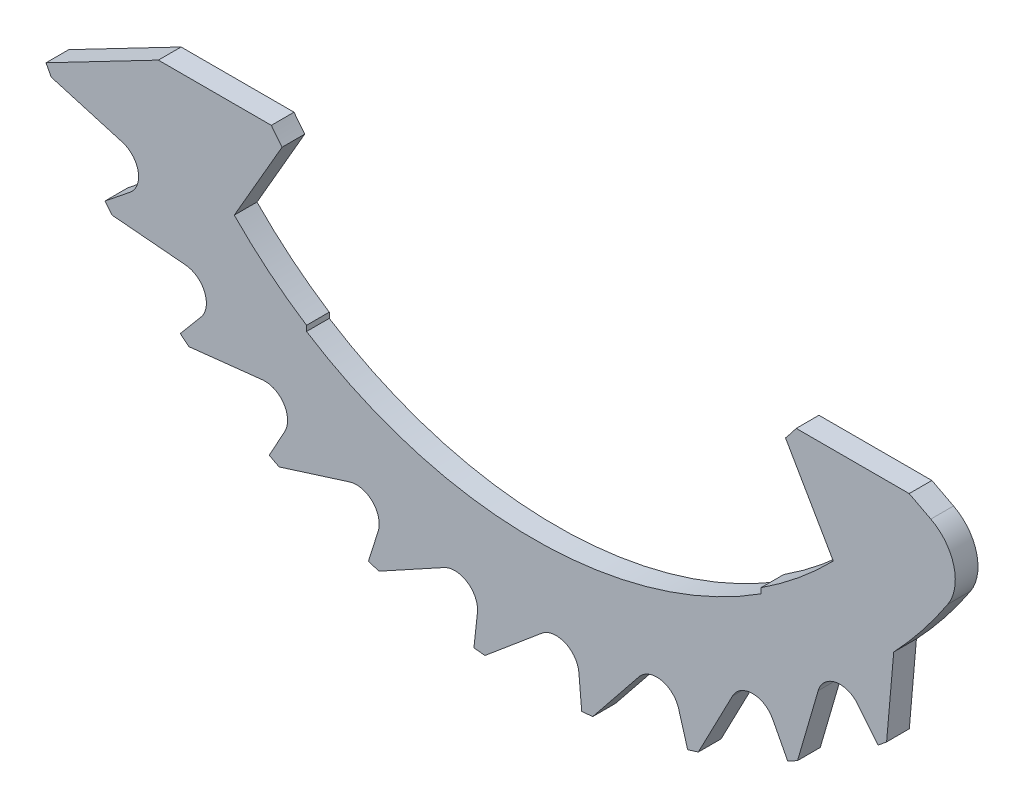
SolidWorks part; units mm, degrees
ref_plane "Front Plane" through (0, 0, 0) normal (0, 0, 1) x (1, 0, 0)
ref_plane "Top Plane" through (0, 0, 0) normal (0, 1, 0) x (1, 0, 0)
ref_plane "Right Plane" through (0, 0, 0) normal (1, 0, 0) x (0, 0, -1)
sketch "Sketch1" plane through (0, 0, 0) normal (0, 0, 1) x (1, 0, 0)
  line L0 (-8.2602, -4.3) -> (-10.7328, -5.5872)
  line L1 (0, 0) -> (0, -12.1) construction
  line L2 (8.2602, -4.3) -> (10.7328, -5.5872)
  line L3 (-5.5392, -4.5997) -> (-6.59, -6.4196)
  line L4 (-8.2602, -4.3) -> (-5.7749, -4.3)
  line L5 (-5, -7.7227) -> (-5, -7.8416)
  line L6 (5.5392, -4.5997) -> (6.59, -6.4196)
  line L8 (-5, 0) -> (-5, -17.1) construction
  line L9 (-5, -17.1) -> (12.3158, -17.1) construction
  line L11 (5, -7.7227) -> (5, -7.8416)
  line L12 (0, -12.1) -> (12.3158, -12.1) construction
  line L13 (5.7749, -4.3) -> (8.2602, -4.3)
  arc A0 (5.7749, -4.3) -> (5.5392, -4.5997) centre (0, 0) cw
  arc A1 (-6.59, -6.4196) -> (-5, -7.7227) centre (0, 0) ccw
  arc A2 (-10.016, -4.3) -> (10.016, -4.3) centre (0, 0) ccw construction
  arc A3 (-10.7328, -5.5872) -> (10.7328, -5.5872) centre (0, 0) ccw
  arc A4 (5, -7.7227) -> (6.59, -6.4196) centre (0, 0) ccw
  circle A5 centre (0, 0) radius 12.1 construction
  circle A6 centre (0, 0) radius 9.2 construction
  arc A7 (-5, -7.8416) -> (5, -7.8416) centre (0, 0) ccw
  arc A8 (-5.7749, -4.3) -> (-5.5392, -4.5997) centre (0, 0) ccw
  point P1 (8.798, 2.6898)
  point P13 (12.1, 0)
  dimension "D1" = 9.3
  dimension "D2" = 9.2
  dimension "D3" = 10.9
  dimension "D10" = 7.2
  dimension "D4" = 2.9
  dimension "D5" = 125
  dimension "D6" = 7.8
  dimension "D9" = 13.18
  dimension "D8" = 30
  dimension "D7" = 10
extrude "Boss-Extrude1" add sketch "Sketch1" along normal blind 0.5
sketch "Sketch2" plane through (0, 0, 0.5) normal (0, 0, 1) x (1, 0, 0)
  line L0 (0, 0) -> (-9.4366, -7.5737) construction
  line L2 (-8.2602, -4.3) -> (-10.7328, -5.5872) construction
  line L3 (-10.6175, -5.8033) -> (-9.0552, -6.2587)
  line L4 (-8.8821, -7.1287) -> (-9.4366, -7.5737)
  arc A0 (-10.7328, -5.5872) -> (10.7328, -5.5872) centre (0, 0) ccw construction
  arc A1 (-8.8901, -6.3068) -> (-8.5007, -6.8226) centre (0, 0) ccw construction
  arc A2 (-8.8821, -7.1287) -> (-9.0552, -6.2587) centre (-9.1951, -6.7387) ccw
  arc A3 (-10.6175, -5.8033) -> (-9.4366, -7.5737) centre (0, 0) ccw
  dimension "D2" = 10.9
  dimension "D3" = 1
  dimension "D1" = 11.25
  dimension "D4" = 55
extrude "Cut-Extrude1" cut sketch "Sketch2" against normal up to next (0.5 mm away)
pattern_circular "CirPattern1" count 10 every 11.25 about axis through (0, 0, 0) along (0, 0, 1) of "Cut-Extrude1"
sketch "Sketch3" plane through (0, 0, 0.5) normal (0, 0, 1) x (1, 0, 0)
  line L0 (7.905, -7.6602) -> (7.7632, -9.2813) construction
  line L1 (0, 0) -> (5.5392, -4.5997) construction
  line L2 (7.92, -7.4889) -> (7.7632, -9.2813)
  line L3 (10.7328, -5.5872) -> (8.2602, -4.3) construction
  line L4 (10.7328, -5.5872) -> (9.6684, -5.0331)
  arc A0 (9.6684, -5.0331) -> (7.92, -7.4889) centre (0, 0) cw
  arc A1 (7.1287, -8.8821) -> (6.2587, -9.0552) centre (6.7387, -9.1951) ccw construction
  arc A4 (8.7245, -7.3207) -> (7.905, -7.6602) centre (8.4031, -7.7037) ccw construction
  arc A5 (9.2691, -7.7777) -> (10.7328, -5.5872) centre (0, 0) ccw construction
  arc A6 (7.7632, -9.2813) -> (10.7328, -5.5872) centre (0, 0) ccw
extrude "Cut-Extrude3" cut sketch "Sketch3" against normal up to next
fillet "Fillet3" radius 1 1 edges at (9.6684, -5.0331, 0.25)
